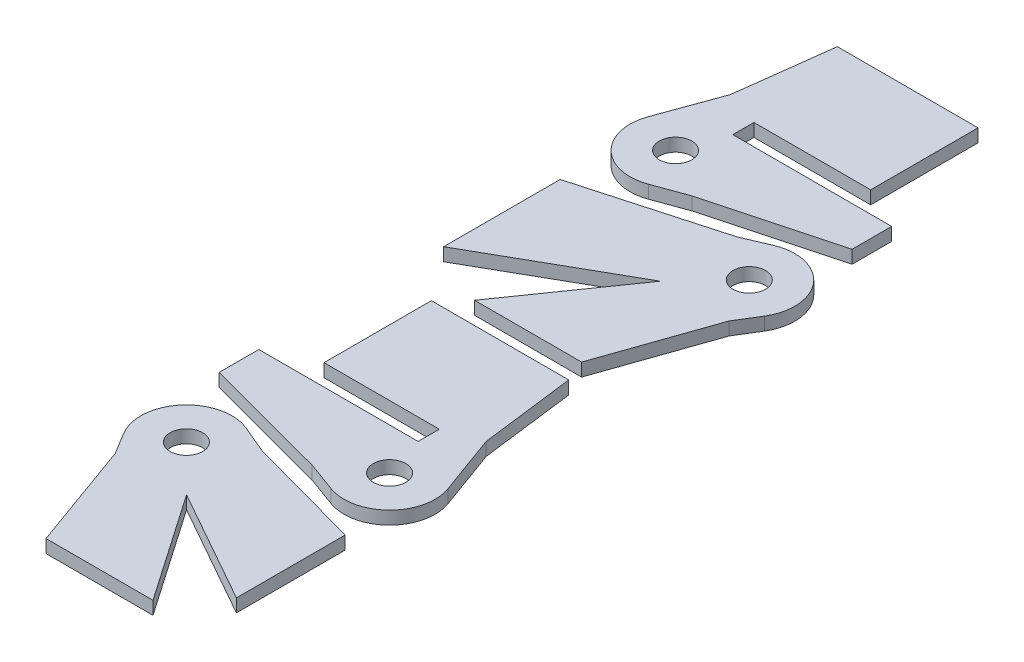
SolidWorks part; units mm, degrees
material "AISI 4130 Steel, normalized at 870C"
ref_plane "Front Plane" through (0, 0, 0) normal (0, 0, 1) x (1, 0, 0)
ref_plane "Top Plane" through (0, 0, 0) normal (0, 1, 0) x (1, 0, 0)
ref_plane "Right Plane" through (0, 0, 0) normal (1, 0, 0) x (0, 0, -1)
sketch "Sketch1" plane through (0, 0, 0) normal (0, 1, 0) x (1, 0, 0)
  line L0 (121.16, 85.8413) -> (125.4255, 97.5606)
  line L1 (125.4255, 97.5606) -> (127.7671, 116.0963)
  line L2 (126.9448, 113.715) -> (155.1851, 113.715) construction
  line L3 (132.4267, 95.1703) -> (155.1851, 95.1703)
  line L4 (132.4267, 95.1703) -> (132.4267, 91.0428)
  line L5 (132.4267, 91.0428) -> (138.7767, 91.0428)
  line L6 (161.0271, 91.0428) -> (161.0271, 82.6862) construction
  line L7 (163.4084, 83.3256) -> (138.7774, 76.7119)
  line L8 (138.7774, 76.7119) -> (132.5544, 74.4469)
  line L9 (125.4255, 97.5606) -> (155.1851, 97.5606) construction
  line L10 (138.7774, 76.7119) -> (138.7774, 86.1846) construction
  line L11 (155.1851, 95.1703) -> (155.1851, 116.0963)
  line L12 (138.7767, 91.0428) -> (163.4084, 91.0428)
  line L13 (123.4717, -18.7401) -> (126.0631, -23.0206)
  line L14 (126.0631, -23.0206) -> (133.6722, -44.1096)
  line L15 (132.813, -41.7283) -> (152.8875, -41.7283) construction
  line L16 (154.5296, -44.1096) -> (139.9867, -23.0206)
  line L17 (139.9867, -23.0206) -> (162.2464, -35.5581)
  line L18 (159.8652, -34.2169) -> (159.8652, -13.6937) construction
  line L19 (162.2464, -14.3461) -> (139.9867, -8.2481)
  line L20 (139.9867, -8.2481) -> (134.5346, -5.9462)
  line L21 (139.9867, -8.2481) -> (139.9867, -23.0206) construction
  line L22 (139.9867, -23.0206) -> (126.0631, -23.0206) construction
  line L23 (155.0794, 76.3074) -> (150.1015, 74.1883)
  line L24 (166.1358, 63.4735) -> (163.5295, 59.2319)
  line L25 (163.5295, 59.2319) -> (156.0894, 37.9044)
  line L26 (156.9201, 40.2856) -> (136.8795, 40.2856) construction
  line L27 (135.2177, 37.9044) -> (150.1015, 59.2319)
  line L28 (150.1015, 59.2319) -> (123.1621, 43.9344)
  line L29 (125.5434, 45.2866) -> (125.5434, 67.3084) construction
  line L30 (123.1621, 66.6413) -> (150.1015, 74.1883)
  line L31 (150.1015, 74.1883) -> (150.1015, 59.2319) construction
  line L32 (163.5295, 59.2319) -> (150.1015, 59.2319) construction
  line L33 (153.0488, -7.8904) -> (147.2011, -5.7621)
  line L34 (147.2011, -5.7621) -> (122.4979, 0.8156)
  line L35 (124.8791, 0.1815) -> (124.8791, 8.5635) construction
  line L36 (122.4979, 8.5635) -> (147.2011, 8.5635)
  line L37 (147.2011, 8.5635) -> (153.5511, 8.5635)
  line L38 (153.5511, 8.5635) -> (153.5511, 12.691)
  line L39 (153.5511, 12.691) -> (131.0767, 12.691)
  line L40 (131.0767, 12.691) -> (131.0767, 33.6315)
  line L41 (131.0767, 31.2503) -> (158.1531, 31.2503) construction
  line L42 (157.8523, 33.6315) -> (160.1778, 15.2233)
  line L43 (160.1778, 15.2233) -> (164.4433, 3.504)
  line L44 (147.2011, 8.5635) -> (147.2011, -5.7621) construction
  line L45 (160.1778, 15.2233) -> (131.0767, 15.2233) construction
  line L46 (123.1621, 43.9344) -> (123.1621, 66.6413)
  line L47 (156.0894, 37.9044) -> (135.2177, 37.9044)
  line L48 (131.0767, 33.6315) -> (157.8523, 33.6315)
  line L49 (122.4979, 0.8156) -> (122.4979, 8.5635)
  line L50 (162.2464, -13.7738) -> (162.2464, 6.7494) construction
  line L51 (132.813, -44.1096) -> (152.8875, -44.1096) construction
  line L52 (163.4084, 91.0428) -> (163.4084, 83.3256)
  line L53 (127.7671, 116.0963) -> (155.1851, 116.0963)
  line L54 (133.6722, -44.1096) -> (154.5296, -44.1096)
  line L55 (162.2464, -35.5581) -> (162.2464, -14.3461)
  line L56 (123.1621, 46.3144) -> (123.1621, 68.3362) construction
  line L57 (126.9448, 116.0963) -> (155.1851, 116.0963) construction
  line L58 (163.4084, 91.0428) -> (163.4084, 82.6862) construction
  line L59 (131.0767, 33.6315) -> (158.1531, 33.6315) construction
  line L60 (122.4979, 0.1815) -> (122.4979, 8.5635) construction
  line L61 (156.9201, 37.9044) -> (136.8795, 37.9044) construction
  line L62 (125.5434, 46.3144) -> (125.5434, 68.3362) construction
  line L63 (159.8652, -13.7738) -> (159.8652, 6.7494) construction
  circle A0 centre (129.5139, 82.8008) radius 3.175
  arc A1 (132.5544, 74.4469) -> (121.16, 85.8413) centre (129.5139, 82.8008) cw
  circle A2 centre (131.0767, -14.1361) radius 3.175
  arc A3 (134.5346, -5.9462) -> (123.4717, -18.7401) centre (131.0767, -14.1361) ccw
  circle A4 centre (158.5616, 68.1278) radius 3.175
  arc A5 (166.1358, 63.4735) -> (155.0794, 76.3074) centre (158.5616, 68.1278) ccw
  circle A6 centre (156.0894, 0.4634) radius 3.175
  arc A7 (164.4433, 3.504) -> (153.0488, -7.8904) centre (156.0894, 0.4634) cw
  dimension "D1" = 6.35
  dimension "D2" = 8.89
  dimension "D3" = 12.4714
  dimension "D16" = 6.35
  dimension "D18" = 8.89
  dimension "D29" = 6.35
  dimension "D30" = 8.89
  dimension "D41" = 6.35
  dimension "D42" = 8.89
  dimension "D4" = 6.223
  dimension "D5" = 110
  dimension "D6" = 82.8
  dimension "D7" = 16.1544
  dimension "D8" = 110
  dimension "D9" = 74.97
  dimension "D10" = 23.0378
  dimension "D11" = 4.1275
  dimension "D12" = 8.3566
  dimension "D13" = 22.2504
  dimension "D14" = 6.35
  dimension "D15" = 22.7584
  dimension "D17" = 97.2
  dimension "D19" = 5.0038
  dimension "D20" = 5.9182
  dimension "D21" = 121.19
  dimension "D22" = 112.89
  dimension "D23" = 70.16
  dimension "D24" = 74.68
  dimension "D25" = 55.41
  dimension "D26" = 60.61
  dimension "D27" = 19.8882
  dimension "D28" = 20.5232
  dimension "D31" = 4.9784
  dimension "D32" = 20.066
  dimension "D33" = 20.0406
  dimension "D34" = 55.09
  dimension "D35" = 5.4102
  dimension "D36" = 113.06
  dimension "D37" = 121.57
  dimension "D38" = 105.65
  dimension "D39" = 60.41
  dimension "D40" = 22.0218
  dimension "D43" = 6.223
  dimension "D44" = 110
  dimension "D45" = 12.4714
  dimension "D46" = 6.35
  dimension "D47" = 4.1275
  dimension "D48" = 110
  dimension "D49" = 82.8
  dimension "D50" = 27.0764
  dimension "D51" = 16.1544
  dimension "D52" = 14.3256
  dimension "D53" = 75.09
  dimension "D54" = 8.382
  dimension "D57" = 20.0745
  dimension "D58" = 23.0798
  dimension "D59" = 22.4197
  dimension "D60" = 25.564
  dimension "D61" = 20.9405
  dimension "D62" = 20.926
  dimension "D63" = 27.9765
  dimension "D64" = 22.588
  dimension "D65" = 20.8717
  dimension "D55" = 2.3813
  dimension "D56" = 2.3813
extrude "Boss-Extrude1" add sketch "Sketch1" along normal blind 2.54
